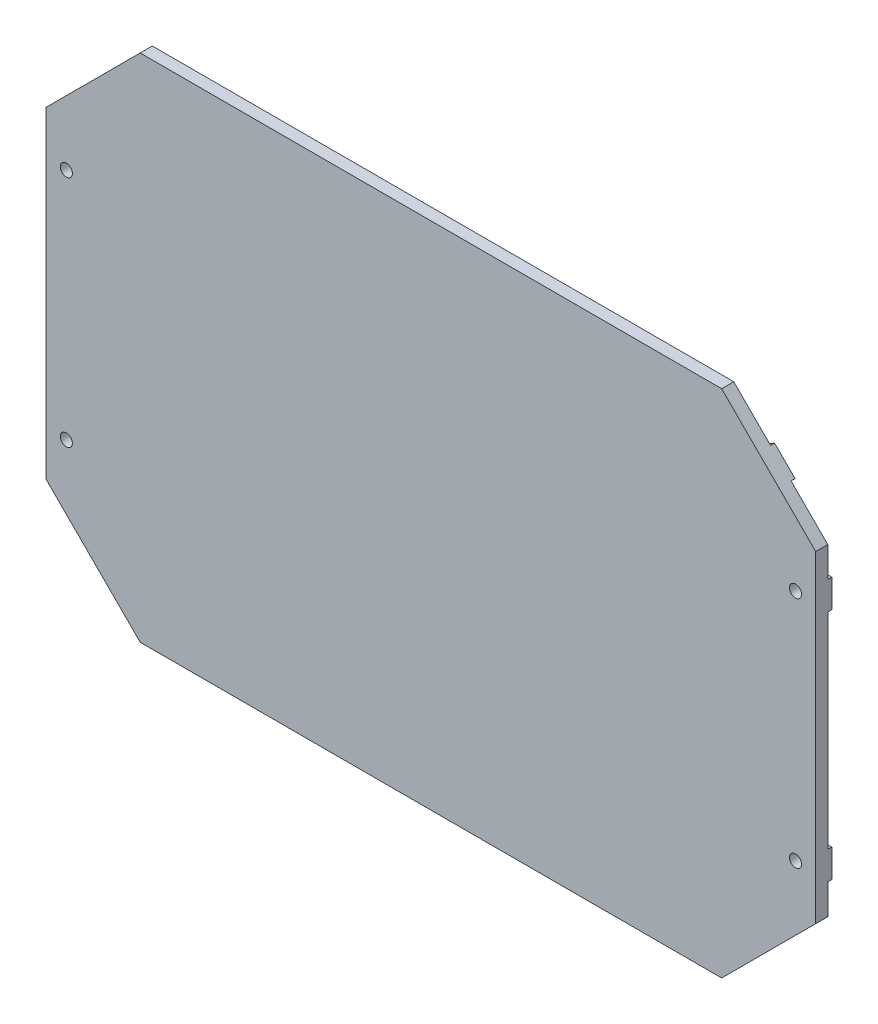
SolidWorks part; units mm, degrees
ref_plane "Front" through (0, 0, 0) normal (0, 0, 1) x (1, 0, 0)
ref_plane "Top" through (0, 0, 0) normal (0, 1, 0) x (1, 0, 0)
ref_plane "Right" through (0, 0, 0) normal (1, 0, 0) x (0, 0, -1)
sketch "Sketch1" plane through (0, 0, 0) normal (0, 0, 1) x (1, 0, 0)
  line L0 (0, 0) -> (-95.5, 0) construction
  line L1 (-95.5, -40) -> (-95.5, 40)
  line L2 (-95.5, 40) -> (-72.1655, 63.3345)
  line L3 (-95.5, -40) -> (-72.1655, -63.3345)
  line L4 (0, 0) -> (0, 18.4839) construction
  line L5 (95.5, -40) -> (72.1655, -63.3345)
  line L6 (95.5, -40) -> (95.5, 40)
  line L7 (95.5, 40) -> (72.1655, 63.3345)
  line L8 (-72.1655, 63.3345) -> (72.1655, 63.3345)
  line L9 (72.1655, -63.3345) -> (-72.1655, -63.3345)
  circle A0 centre (-90.5, 29) radius 1.5
  circle A1 centre (-90.5, -29) radius 1.5
  circle A2 centre (90.5, -29) radius 1.5
  circle A3 centre (90.5, 29) radius 1.5
  dimension "D7" = 3
  dimension "D8" = 3
  dimension "D1" = 80
  dimension "D2" = 95.5
  dimension "D3" = 33
  dimension "D4" = 33
  dimension "D5" = 135
  dimension "D6" = 135
  dimension "D9" = 11
  dimension "D10" = 5
  dimension "D11" = 11
extrude "Boss-Extrude1" add sketch "Sketch1" along normal blind 3
sketch "Sketch2" plane through (0, 0, 0) normal (0, 0, -1) x (-1, 0, 0)
  line L0 (-83.8327, 51.6673) -> (83.8327, -51.6673) construction
  line L1 (83.8327, 51.6673) -> (-83.8327, -51.6673) construction
  line L5 (-95.5, 40) -> (-72.1655, 63.3345) construction
  line L6 (0, 0) -> (13.3416, 0) construction
  line L8 (72.1655, 63.3345) -> (95.5, 40) construction
  line L9 (-72.1655, -63.3345) -> (-95.5, -40) construction
  line L10 (81.2891, 54.2109) -> (-86.3764, -49.1236)
  line L11 (86.3764, 49.1236) -> (-81.2891, -54.2109)
  line L12 (72.1655, 63.3345) -> (95.5, 40)
  line L13 (-72.1655, -63.3345) -> (-95.5, -40)
  line L14 (95.5, -40) -> (72.1655, -63.3345) construction
  line L15 (-86.3764, 49.1236) -> (81.2891, -54.2109)
  line L16 (-81.2891, 54.2109) -> (86.3764, -49.1236)
  line L17 (95.5, -40) -> (72.1655, -63.3345)
  line L18 (-95.5, 40) -> (-72.1655, 63.3345)
  line L19 (-85.6691, 48.6877) -> (81.9964, -54.6468) construction
  line L20 (-81.9964, 54.6468) -> (85.6691, -48.6877) construction
  line L21 (81.9964, 54.6468) -> (-85.6691, -48.6877) construction
  line L22 (85.6691, 48.6877) -> (-81.9964, -54.6468) construction
  line L23 (-95.5, -40) -> (-95.5, 40) construction
  line L24 (-95.5, -25.5) -> (95.5, -25.5)
  line L25 (-95.5, -25.5) -> (-95.5, -32.5)
  line L26 (-95.5, -32.5) -> (95.5, -32.5)
  line L27 (95.5, -25.5) -> (95.5, -32.5)
  line L28 (-95.5, -25.5) -> (95.5, -32.5) construction
  line L29 (-95.5, -32.5) -> (95.5, -25.5) construction
  line L30 (95.5, 40) -> (95.5, -40) construction
  line L32 (-95.5, 32.5) -> (95.5, 32.5)
  line L33 (-95.5, 32.5) -> (-95.5, 25.5)
  line L34 (-95.5, 25.5) -> (95.5, 25.5)
  line L35 (95.5, 32.5) -> (95.5, 25.5)
  line L36 (-95.5, 32.5) -> (95.5, 25.5) construction
  line L37 (-95.5, 25.5) -> (95.5, 32.5) construction
  point P37 (0, -29)
  point P46 (0, 29)
  circle M14 centre (-90.5, -29) radius 1.5
  circle M15 centre (90.5, 29) radius 1.5
  line M16 (72.1655, -63.3345) -> (95.5, -40)
  line M17 (95.5, -40) -> (95.5, 40)
  line M18 (95.5, 40) -> (72.1655, 63.3345)
  line M20 (-72.1655, 63.3345) -> (-95.5, 40)
  line M21 (-95.5, 40) -> (-95.5, -40)
  line M22 (-95.5, -40) -> (-72.1655, -63.3345)
  circle M24 centre (90.5, -29) radius 1.5
  circle M25 centre (-90.5, 29) radius 1.5
  dimension "D6" = 7.5
  dimension "D1" = 3.5
  dimension "D2" = 3.5
  dimension "D3" = 7
  dimension "D4" = 3.5
  dimension "D7" = 7.5
  dimension "D8" = 7
  dimension "D5" = 3.5
extrude "Boss-Extrude2" add sketch "Sketch2" along normal blind 1 contours L15 L32 L16 M20 | L15 L34 L16 L32 | L34 L15 L32 M21 M25 | L16 L34 L10 L32 | L10 L34 L11 L32 | L10 L32 L11 M18 | L11 L34 L32 M17 M15 | L34 L15 L10 L16 | L34 L10 L16 L11 | L16 L10 L15 L11 | L15 L24 L16 L11 | L10 L24 L11 L15 | L10 L26 L11 L24 | L26 L10 L24 M21 M14 | L11 L26 L15 L24 | L15 L26 L16 L24 | L16 L26 L24 M17 M24 | L26 L15 L16 M16 | L26 L10 L11 M22
